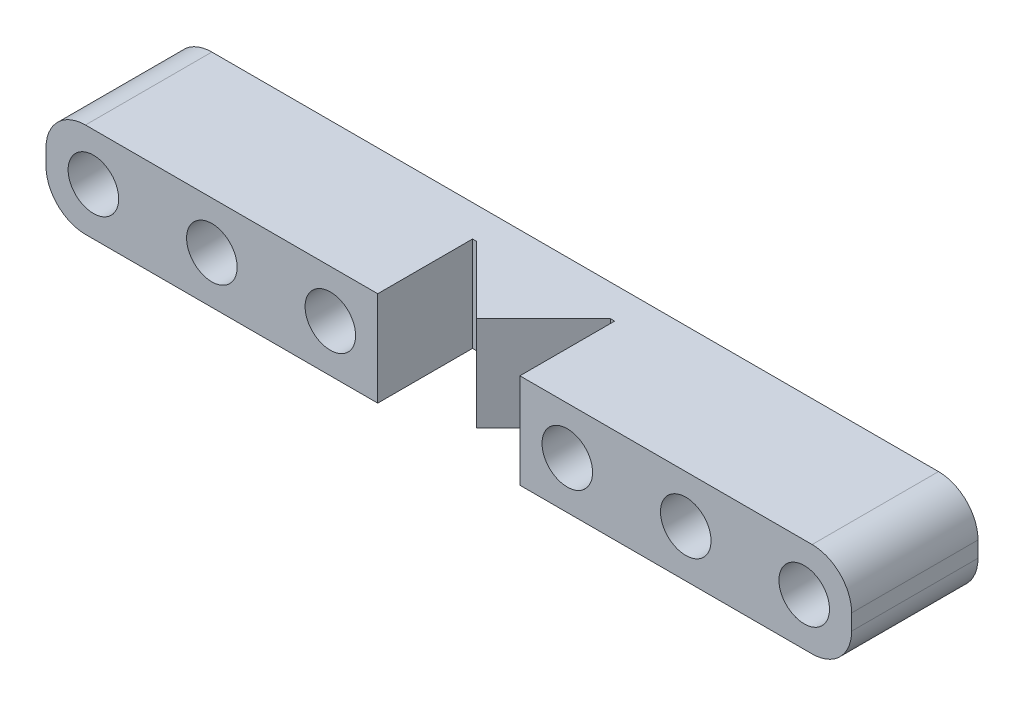
SolidWorks part; units mm, degrees
ref_plane "Front Plane" through (0, 0, 0) normal (0, 0, 1) x (1, 0, 0)
ref_plane "Top Plane" through (0, 0, 0) normal (0, 1, 0) x (1, 0, 0)
ref_plane "Right Plane" through (0, 0, 0) normal (1, 0, 0) x (0, 0, -1)
sketch "Sketch1" plane through (0, 0, 0) normal (0, 0, 1) x (1, 0, 0)
  line L1 (-0.5, 3) -> (15.5, 3)
  line L2 (-3, 0.5) -> (-3, -0.5)
  line L3 (-0.5, -3) -> (15.5, -3)
  line L4 (18, 0.5) -> (18, -0.5)
  circle A0 centre (0, 0) radius 1.6
  circle A1 centre (15, 0) radius 1.6
  arc A2 (15.5, -3) -> (18, -0.5) centre (15.5, -0.5) ccw
  arc A3 (15.5, 3) -> (18, 0.5) centre (15.5, 0.5) cw
  arc A4 (-3, -0.5) -> (-0.5, -3) centre (-0.5, -0.5) ccw
  arc A5 (-0.5, 3) -> (-3, 0.5) centre (-0.5, 0.5) ccw
  point P13 (18, 3)
  point P18 (-3, 3)
  dimension "D1" = 3.2
  dimension "D5" = 3.2
  dimension "D6" = 3
  dimension "D9" = 2.5
  dimension "D2" = 3
  dimension "D3" = 3
  dimension "D4" = 3
  dimension "D7" = 3
  dimension "D8" = 21
extrude "Boss-Extrude1" add sketch "Sketch1" along normal blind 8
sketch "Sketch2" plane through (0, -3, 0) normal (0, -1, 0) x (1, 0, 0)
  line L0 (18, 8) -> (18, 0) construction
  line L1 (3, 10.1997) -> (12, 10.1997)
  line L2 (3, 10.1997) -> (3, 2)
  line L3 (3, 2) -> (12, 2)
  line L4 (12, 10.1997) -> (12, 2)
  line L5 (-3, 8) -> (-3, 0) construction
  line L6 (-0.5, 0) -> (15.5, 0) construction
  dimension "D1" = 6
  dimension "D2" = 6
  dimension "D3" = 2
extrude "Cut-Extrude1" cut sketch "Sketch2" against normal blind 8
sketch "Sketch3" plane through (0, -3, 0) normal (0, -1, 0) x (1, 0, 0)
  line L0 (3.2574, 2) -> (7.5, 6.2426)
  line L1 (3, 2) -> (12, 2) construction
  line L2 (7.5, 6.2426) -> (11.7426, 2)
  line L3 (11.7426, 2) -> (3.2574, 2)
  line L5 (-0.5, 0) -> (15.5, 0) construction
  point P4 (10.1425, 7.1892)
  point P6 (8.9245, 7.818)
  point P7 (0, 0)
  point P10 (7.5, 0)
  point P11 (9, 6.874)
  dimension "D1" = 90
  dimension "D2" = 45
  dimension "D3" = 6
extrude "Boss-Extrude2" add sketch "Sketch3" against normal up to surface (6 mm away) up to face at (7.5, 3, 4.5)
sketch "Sketch4" plane through (0, 0, 0) normal (0, 0, -1) x (-1, 0, 0)
  line L0 (-3, 3) -> (0.5, 3) construction
  line L1 (0.5, 3) -> (15.5, 3)
  line L3 (0.5, -3) -> (15.5, -3)
  line L4 (18, 0.5) -> (18, -0.5)
  line L5 (-7.5, 3) -> (-7.5, 8.5491) construction
  line L6 (-33, 0.5) -> (-33, -0.5)
  line L7 (-15.5, -3) -> (-30.5, -3)
  line L8 (-15.5, 3) -> (-30.5, 3)
  arc A0 (3, 0.5) -> (0.5, 3) centre (0.5, 0.5) ccw construction
  circle A1 centre (7.5, 0) radius 1.6
  arc A2 (15.5, -3) -> (18, -0.5) centre (15.5, -0.5) ccw
  arc A3 (15.5, 3) -> (18, 0.5) centre (15.5, 0.5) cw
  circle A4 centre (-30, 0) radius 1.6
  arc A5 (-30.5, 3) -> (-33, 0.5) centre (-30.5, 0.5) ccw
  circle A8 centre (15, 0) radius 1.6
  arc A9 (-30.5, -3) -> (-33, -0.5) centre (-30.5, -0.5) cw
  circle A10 centre (-22.5, 0) radius 1.6
  dimension "D1" = 3.2
  dimension "D3" = 2.5
  dimension "D2" = 7.5
  dimension "D4" = 2
  dimension "D5" = 3
extrude "Boss-Extrude3" add sketch "Sketch4" against normal blind 8
